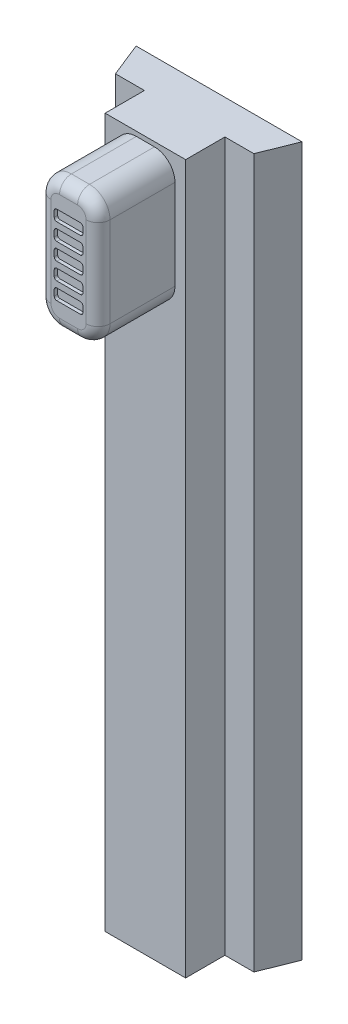
SolidWorks part; units mm, degrees
ref_plane "Front Plane" through (0, 0, 0) normal (0, 0, 1) x (1, 0, 0)
ref_plane "Top Plane" through (0, 0, 0) normal (0, 1, 0) x (1, 0, 0)
ref_plane "Right Plane" through (0, 0, 0) normal (1, 0, 0) x (0, 0, -1)
sketch "Sketch1" plane through (0, 0, 0) normal (0, 1, 0) x (1, 0, 0)
  line L0 (0.8787, -0.345) -> (5.5916, -0.345)
  line L1 (0.8787, 1.955) -> (0.8787, -0.345)
  line L3 (-0.8185, 1.955) -> (-1.6213, 3.9663)
  line L4 (-0.8185, 1.955) -> (0.8787, 1.955)
  line L6 (8.0916, 3.9663) -> (-1.6213, 3.9663)
  line L9 (7.2888, 1.955) -> (5.5916, 1.955)
  line L10 (7.2888, 1.955) -> (8.0916, 3.9663)
  line L12 (5.5916, 1.955) -> (5.5916, -0.345)
  point P12 (3.2352, 3.9663)
extrude "Boss-Extrude1" add sketch "Sketch1" along normal blind 41.5
sketch "Sketch2" plane through (0, 0, 0.345) normal (0, 0, 1) x (1, 0, 0)
  line L3 (4.9647, 33.5646) -> (1.5056, 33.5646)
  line L4 (4.9647, 33.5646) -> (4.9647, 41.2339)
  line L5 (4.9647, 41.2339) -> (1.5056, 41.2339)
  line L6 (1.5056, 33.5646) -> (1.5056, 41.2339)
  line L7 (4.9647, 33.5646) -> (1.5056, 41.2339) construction
  line L8 (4.9647, 41.2339) -> (1.5056, 33.5646) construction
extrude "Boss-Extrude2" add sketch "Sketch2" along normal blind 4.5
fillet "Fillet1" radius 1.2 4 edges at (4.9647, 41.2339, 2.595) (1.5056, 41.2339, 2.595) (1.5056, 33.5646, 2.595) (4.9647, 33.5646, 2.595)
fillet "Fillet2" radius 0.7 8 edges at (4.6132, 33.9161, 4.845) (3.2352, 33.5646, 4.845) (1.8571, 33.9161, 4.845) (1.5056, 37.3993, 4.845) (1.8571, 40.8824, 4.845) (3.2352, 41.2339, 4.845) (4.6132, 40.8824, 4.845) (4.9647, 37.3993, 4.845)
sketch "Sketch3" plane through (0, 0, 4.845) normal (0, 0, 1) x (1, 0, 0)
  line L4 (4.0734, 37.0769) -> (2.3969, 37.0769)
  line L5 (4.0734, 37.0769) -> (4.0734, 37.7216)
  line L6 (4.0734, 37.7216) -> (2.3969, 37.7216)
  line L7 (2.3969, 37.0769) -> (2.3969, 37.7216)
  line L8 (4.0734, 37.0769) -> (2.3969, 37.7216) construction
  line L9 (4.0734, 37.7216) -> (2.3969, 37.0769) construction
  point P6 (3.2352, 37.3993)
extrude "Cut-Extrude1" cut sketch "Sketch3" against normal blind 0.2
fillet "Fillet3" radius 0.15 4 edges at (4.0734, 37.7216, 4.745) (4.0734, 37.0769, 4.745) (2.3969, 37.0769, 4.745) (2.3969, 37.7216, 4.745)
pattern_linear "LPattern1" count 3 spacing 1 along (0, 1, 0) count 3 spacing 1 along (0, -1, 0) of "Fillet3", "Cut-Extrude1"
